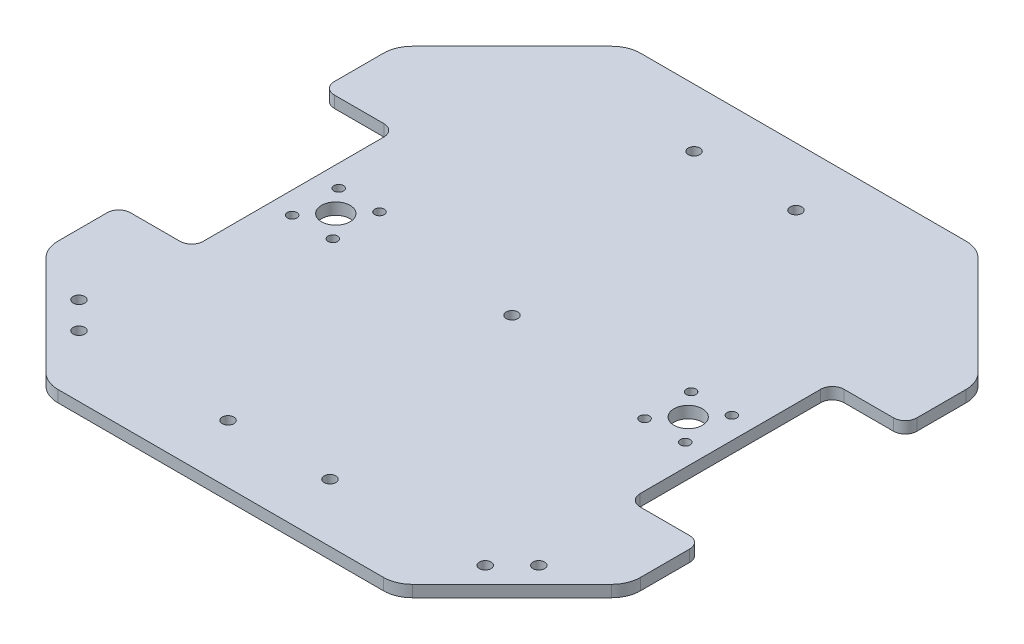
SolidWorks part; units mm, degrees
ref_plane "前视基准面" through (0, 0, 0) normal (0, 0, 1) x (1, 0, 0)
ref_plane "上视基准面" through (0, 0, 0) normal (0, 1, 0) x (1, 0, 0)
ref_plane "右视基准面" through (0, 0, 0) normal (1, 0, 0) x (0, 0, -1)
other "Configuration Table"
sketch "草图1" plane through (0, 0, 0) normal (0, 1, 0) x (1, 0, 0)
  line L0 (-227.5051, 0) -> (214.8307, 0) construction
  line L1 (0, -181.0695) -> (0, 185.6337) construction
  line L2 (60, 100) -> (-60, 100)
  line L3 (-60, 100) -> (-100, 60)
  line L4 (-100, 60) -> (-100, 35)
  line L5 (-100, 35) -> (-75, 35)
  line L6 (-75, 35) -> (-75, -35)
  line L7 (75, 35) -> (75, -35)
  line L8 (100, 35) -> (75, 35)
  line L9 (100, 60) -> (100, 35)
  line L10 (60, 100) -> (100, 60)
  line L11 (100, -35) -> (75, -35)
  line L12 (100, -60) -> (100, -35)
  line L13 (60, -100) -> (100, -60)
  line L14 (60, -100) -> (-60, -100)
  line L15 (-60, -100) -> (-100, -60)
  line L16 (-100, -60) -> (-100, -35)
  line L17 (-100, -35) -> (-75, -35)
  point P15 (0, 100)
  point P16 (75, 0)
  point P24 (-75, 0)
  dimension "D1" = 35
  dimension "D2" = 100
  dimension "D3" = 100
  dimension "D4" = 60
  dimension "D5" = 25
  dimension "D6" = 25
extrude "凸台-拉伸1" add sketch "草图1" along normal blind 4
fillet "圆角1" radius 4 8 edges at (75, 2, 35) (75, 2, -35) (-75, 2, 35) (-75, 2, -35) (-100, 2, -35) (-100, 2, 35) (100, 2, 35) (100, 2, -35)
fillet "圆角2" radius 10 8 edges at (100, 2, 60) (60, 2, 100) (-60, 2, 100) (-100, 2, 60) (100, 2, -60) (60, 2, -100) (-60, 2, -100) (-100, 2, -60)
sketch "草图8" plane through (0, 4, 0) normal (0, 1, 0) x (1, 0, 0)
  line L0 (-75, 0) -> (-60.5, 0) construction
  line L1 (-75, 31) -> (-75, -31) construction
  line L2 (-60.5, 0) -> (-60.5, 8) construction
  line L3 (-60.5, 8) -> (-67.5, 8) construction
  line L4 (0, 100) -> (0, -100) construction
  line L5 (55.8579, 100) -> (-55.8579, 100) construction
  line L6 (-55.8579, -100) -> (55.8579, -100) construction
  line L7 (0, 80) -> (-17.5, 80) construction
  line L8 (0, 0) -> (-80, -80) construction
  line L9 (-97.0711, -62.9289) -> (-62.9289, -97.0711) construction
  line L10 (-74.3431, -74.3431) -> (-78.9393, -69.747) construction
  circle A0 centre (-60.5, 0) radius 4.9
  circle A1 centre (-67.5, 8) radius 1.65
  circle A2 centre (-53.5, 8) radius 1.65
  circle A3 centre (-53.5, -8) radius 1.65
  circle A4 centre (-67.5, -8) radius 1.65
  circle A5 centre (53.5, -8) radius 1.65
  circle A6 centre (67.5, -8) radius 1.65
  circle A7 centre (60.5, 0) radius 4.9
  circle A8 centre (53.5, 8) radius 1.65
  circle A9 centre (67.5, 8) radius 1.65
  circle A10 centre (-17.5, 80) radius 2
  circle A11 centre (17.5, 80) radius 2
  circle A12 centre (17.5, -80) radius 2
  circle A13 centre (-17.5, -80) radius 2
  circle A14 centre (0, 0) radius 2
  circle A15 centre (-78.9393, -69.747) radius 2
  circle A16 centre (-69.747, -78.9393) radius 2
  circle A17 centre (69.747, -78.9393) radius 2
  circle A18 centre (78.9393, -69.747) radius 2
  point P8 (-67.5, 8)
  point P32 (0, 80)
  dimension "D4" = 80
  dimension "D6" = 4
  dimension "D7" = 4
  dimension "D10" = 4
  dimension "D1" = 14.5
  dimension "D2" = 8
  dimension "D3" = 7
  dimension "D5" = 17.5
  dimension "D8" = 6.5
  dimension "D9" = 8
extrude "切除-拉伸1" cut sketch "草图8" against normal through all
